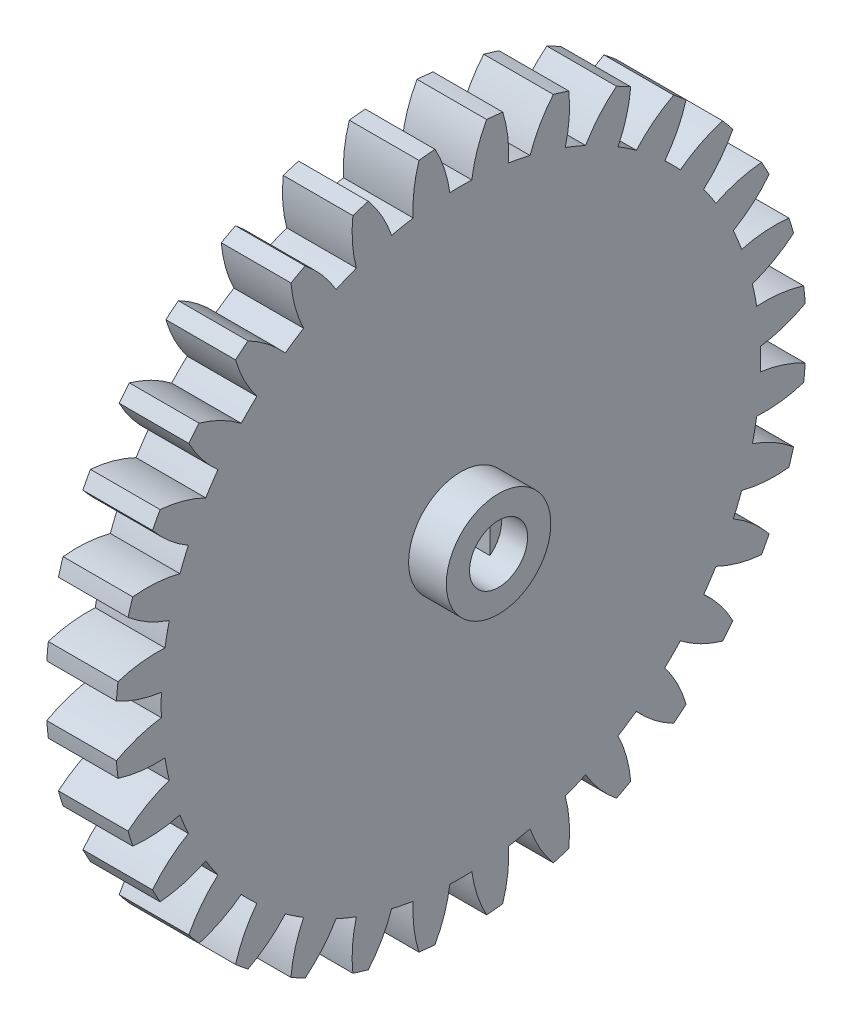
SolidWorks part; units mm, degrees
ref_plane "Plane1" through (0, 0, 0) normal (0, 0, 1) x (1, 0, 0)
ref_plane "Plane2" through (0, 0, 0) normal (0, 1, 0) x (1, 0, 0)
ref_plane "Plane3" through (0, 0, 0) normal (1, 0, 0) x (0, 0, -1)
sketch "HoldingSke" plane through (0, 0, 0) normal (0, 1, 0) x (1, 0, 0)
  line L0 (0, 0) -> (0.4846, -0.3028)
  line L1 (-15, 0) -> (100, 0) construction
  line L2 (0, 0) -> (-2.1039, 2.3779)
  line L3 (0, 0) -> (-11.863, 4.5341)
  line L4 (0, 0) -> (7.3237, 4.5764)
  line L5 (0, 0) -> (-46.8476, -17.4728)
  line L6 (0, 0) -> (-4.9738, -3.3558)
  line L7 (-2.1039, 2.3779) -> (8.6586, 51.2059)
  line L8 (-76.2, 54.61) -> (-76.1, 54.61)
  line L9 (-67.7845, 28.3722) -> (-49.3413, 33.142)
  line L10 (-76.2, 71.12) -> (104.1128, 71.12)
  line L11 (0, 0) -> (-6, 0)
  line L12 (-76.2, 101.6) -> (-76.147, 101.6)
  line L13 (24.9733, 27.94) -> (52.9518, 28.4284)
  line L14 (24.9733, 27.94) -> (24.9743, 27.94)
  line L15 (24.9733, 27.94) -> (100.4006, 29.5858)
  line L16 (-63.627, -1.75) -> (-12.827, -1.75)
  circle A0 centre (0, 0) radius 0.4
  circle A1 centre (0, 0) radius 25.8115
  circle A2 centre (0, 0) radius 37.5
  circle A3 centre (0, 0) radius 0.4
  dimension "MHD" = 51.623
  dimension "Hub_dia" = 75
  dimension "Bore" = 0.8
  dimension "MBD" = 0.8
  dimension "Num_teeth" = 32
  dimension "Pitch" = 0.5714
  dimension "Overall_len" = 50
  dimension "Show_teeth" = 32
  dimension "Thickness" = 6
  dimension "OAL" = 50.0001
  dimension "T_dim" = 0.1
  dimension "Ap" = 14.5
  dimension "H" = 19.05
  dimension "Pitch_radius" = 180.3128
  dimension "Width" = 6
  dimension "Backlash" = 0.053
  dimension "Addendum_fac" = 1
  dimension "Dedendum_fac" = 1.25
  dimension "Clearance_fac" = 0.25
  dimension "Dedendum_add" = 0.001
  dimension "Module" = 1.75
sketch "BasProSke" plane through (0, 0, 0) normal (0, 1, 0) x (1, 0, 0)
  line L0 (-10, 0) -> (60, 0) construction
  line L1 (0, 0) -> (0, 29.75)
  line L2 (0, 0) -> (6, 0)
  line L3 (6, 0) -> (6, 29.75)
  line L4 (6, 29.75) -> (0, 29.75)
  dimension "Thickness" = 6
  dimension "Diameter" = 59.5
revolve "Base-Revolve" add sketch "BasProSke" angle 360 about L0
sketch "TooCutSke" plane through (0, 0, 0) normal (1, 0, 0) x (0, 0, -1)
  line L1 (0, 0) -> (0, 107) construction
  line L2 (0, 0) -> (-1.4666, 27.9616) construction
  line L3 (0, 0) -> (-5.4832, 55.672) construction
  line L4 (-1.4666, 27.9616) -> (-2.7416, 27.836) construction
  arc A0 (0.9481, 25.7941) -> (-0.9481, 25.7941) centre (0, 0) ccw
  arc A1 (2.2372, 29.6912) -> (-2.2372, 29.6912) centre (0, 0) ccw
  circle A2 centre (0, 0) radius 28 construction
  circle A3 centre (0, 0) radius 27.1081 construction
  arc A4 (-0.9481, 25.7941) -> (-2.2372, 29.6912) centre (-12.0459, 24.2847) ccw
  arc A5 (2.2372, 29.6912) -> (0.9481, 25.7941) centre (12.0459, 24.2847) ccw
  dimension "Root_dia" = 51.623
  dimension "Overcut_dia" = 59.5508
  dimension "Pitch_dia" = 56
  dimension "Base_dia" = 54.2163
  dimension "Flank_rad" = 11.2
  dimension "Half_ang" = 5.625
  dimension "Half_CT" = 1.2811
extrude "ToothCut" cut sketch "TooCutSke" along normal through all
fillet "Breaks" [suppressed] radius 0.035
fillet "RootFillets" [suppressed] radius 0.4385
pattern_circular "TeethCuts" count 32 every 11.25 about axis through (-10, 0, 0) along (1, 0, 0) of "ToothCut", "RootFillets", "Breaks"
sketch "HubNeaOneSke" plane through (0, 0, 0) normal (-1, 0, 0) x (0, 0, 1)
  circle A0 centre (0, 0) radius 25.8115
  dimension "Diameter" = 51.623
extrude "HubNearOne" [suppressed] add sketch "HubNeaOneSke" along normal blind 44.0001
sketch "HubNeaBotSke" plane through (0, 0, 0) normal (-1, 0, 0) x (0, 0, 1)
  circle A0 centre (0, 0) radius 25.8115
  dimension "Diameter" = 51.623
extrude "HubNearBoth" [suppressed] add sketch "HubNeaBotSke" along normal blind 22
ref_plane "FarPln" through (6, 0, 0) normal (1, 0, 0) x (0, 0, -1)
sketch "HubFarSke" plane through (6, 0, 0) normal (1, 0, 0) x (0, 0, -1)
  circle A0 centre (0, 0) radius 25.8115
  dimension "Diameter" = 51.623
extrude "HubFar" [suppressed] add sketch "HubFarSke" along normal blind 22
sketch "BorSke" plane through (0, 0, 0) normal (1, 0, 0) x (0, 0, -1)
  circle A0 centre (0, 0) radius 0.4
  dimension "Diameter" = 0.8
extrude "Bore" cut sketch "BorSke" along normal mid plane 100.0001
sketch "KeySke" plane through (0, 0, 0) normal (1, 0, 0) x (0, 0, -1)
  line L0 (-0.05, 0) -> (-0.05, 0.5)
  line L1 (-0.05, 0.5) -> (0.05, 0.5)
  line L2 (0.05, 0.5) -> (0.05, 0)
  line L3 (0, 0) -> (0, 34) construction
  line L4 (-0.05, 0) -> (0.05, 0)
  dimension "Offset" = 0.5
  dimension "Width" = 0.1
extrude "Keyway" [suppressed] cut sketch "KeySke" along normal mid plane 100.0001
pattern_circular "Keyway2" [suppressed] count 2 every 90 about axis through (-10, 0, 0) along (1, 0, 0)
sketch "Sketch2" plane through (6, 0, 0) normal (1, 0, 0) x (0, 0, -1)
  circle A0 centre (0, 0) radius 4.5
  dimension "D1" = 9
extrude "Boss-Extrude1" add sketch "Sketch2" along normal blind 3.25
sketch "Sketch3" plane through (9.25, 0, 0) normal (1, 0, 0) x (0, 0, -1)
  circle A0 centre (0, 0) radius 2.5
extrude "Cut-Extrude1" cut sketch "Sketch3" against normal blind 2.25
sketch "Sketch5" plane through (7, 0, 0) normal (1, 0, 0) x (0, 0, -1)
  line L0 (-1.4999, 2.0001) -> (-1.5001, -1.9999)
  line L1 (1.5001, 1.9999) -> (1.4999, -2.0001)
  circle A0 centre (0, 0) radius 2.5
  circle M3 centre (0, 0) radius 2.5
  dimension "D1" = 5
  dimension "D2" = 3
extrude "Cut-Extrude3" cut sketch "Sketch5" against normal blind 6 contours L1 L0 M3
equation "' \"Module@HoldingSke\" = 6.35"
equation "' \"Num_teeth@HoldingSke\" = 12"
equation "' \"Ap@HoldingSke\" =  20"
equation "' \"Ap@HoldingSke\" = 20"
equation "' \"Width@HoldingSke\" = 0.5 * 25.4"
equation "' \"Hub_dia@HoldingSke\"= 1 * 25.4"
equation "' \"Hub_dia@HoldingSke\" = 1 * 25.4"
equation "' \"Overall_len@HoldingSke\" = 1.0 * 25.4"
equation "' \"Bore@HoldingSke\" = 0.75 * 25.4"
equation "' \"T_dim@HoldingSke\" = 0.1 * 25.4"
equation "' \"Width@KeySke\" = 0.25 * 25.4"
equation "' \"Show_teeth@HoldingSke\" = 13"
equation "' \"Backlash@HoldingSke\" = 0.009 * 25.4"
equation "' \"Addendum_fac@HoldingSke\" = 1.0"
equation "' \"Dedendum_fac@HoldingSke\" = 1.25"
equation "' \"Dedendum_add@HoldingSke\" = 0.00005 * 25.4"
equation "' \"Clearance_fac@HoldingSke\" = 0.25"
equation "\"Pitch@HoldingSke\" = 1 / \"Module@HoldingSke\""
equation "\"Overcut_dia@TooCutSke\" = (\"Num_teeth@HoldingSke\" + 2 * \"Addendum_fac@HoldingSke\") / \"Pitch@HoldingSke\" + 0.002 * 25.4"
equation "\"Pitch_dia@TooCutSke\" = \"Num_teeth@HoldingSke\" / \"Pitch@HoldingSke\""
equation "\"Base_dia@TooCutSke\" = \"Num_teeth@HoldingSke\" / \"Pitch@HoldingSke\" * cos((\"Ap@HoldingSke\"  * 3.14159265 / 180))"
equation "\"Root_dia@TooCutSke\" = (\"Num_teeth@HoldingSke\" + 2) / \"Pitch@HoldingSke\" - 2 * (\"Addendum_fac@HoldingSke\" + \"Dedendum_fac@HoldingSke\") / \"Pitch@HoldingSke\" - \"Dedendum_add@HoldingSke\" * 2"
equation "\"Half_ang@TooCutSke\" = 180 / \"Num_teeth@HoldingSke\""
equation "\"Half_CT@TooCutSke\" = \"Num_teeth@HoldingSke\" / \"Pitch@HoldingSke\" * sin((3.14159265 / 2 / \"Num_teeth@HoldingSke\")) / 2 - 7 * \"Backlash@HoldingSke\" / 4"
equation "\"Flank_rad@TooCutSke\" = \"Num_teeth@HoldingSke\" / \"Pitch@HoldingSke\" / 5"
equation "\"Radius@RootFillets\" = \"Clearance_fac@HoldingSke\" / \"Pitch@HoldingSke\" + \"Dedendum_add@HoldingSke\""
equation "\"Break_rad@Breaks\" = 0.02 / \"Pitch@HoldingSke\""
equation "\"Thickness@HoldingSke\" = \"Width@HoldingSke\""
equation "\"OAL@HoldingSke\" = \"Thickness@HoldingSke\""
equation "\"MHD@HoldingSke\" = (\"Num_teeth@HoldingSke\" + 2) / \"Pitch@HoldingSke\" - 2 * (\"Addendum_fac@HoldingSke\" + \"Dedendum_fac@HoldingSke\")  / \"Pitch@HoldingSke\" - \"Dedendum_add@HoldingSke\" * 2"
equation "\"MBD@HoldingSke\" = (\"Num_teeth@HoldingSke\" + 2) / \"Pitch@HoldingSke\" - 2 * (\"Addendum_fac@HoldingSke\" + \"Dedendum_fac@HoldingSke\")  / \"Pitch@HoldingSke\" - \"Dedendum_add@HoldingSke\" * 2 - 0.002 * 25.4"
equation "\"MHD@HoldingSke\" = ((sgn( \"MHD@HoldingSke\" - \"Hub_dia@HoldingSke\" )-1)*( \"MHD@HoldingSke\" - \"Hub_dia@HoldingSke\" ))/-2+ \"Hub_dia@HoldingSke\""
equation "\"MBD@HoldingSke\" = ((sgn( \"MBD@HoldingSke\" - \"Bore@HoldingSke\" )-1)*( \"MBD@HoldingSke\" - \"Bore@HoldingSke\" ))/-2+ \"Bore@HoldingSke\""
equation "\"OAL@HoldingSke\" = ((sgn( \"OAL@HoldingSke\" - \"Overall_len@HoldingSke\" )+1)*( \"OAL@HoldingSke\" - \"Overall_len@HoldingSke\" ))/2 + \"Overall_len@HoldingSke\" + 0.000002 * 25.4"
equation "\"Num_teeth@TeethCuts\" = int( \"Show_teeth@HoldingSke\" ) + 1"
equation "\"Num_teeth@TeethCuts\" = ((sgn( \"Num_teeth@TeethCuts\" - \"Num_teeth@HoldingSke\" )-1)*( \"Num_teeth@TeethCuts\" - \"Num_teeth@HoldingSke\" ))/-2+ \"Num_teeth@HoldingSke\""
equation "\"Num_teeth@TeethCuts\" = ((sgn( \"Num_teeth@TeethCuts\" - 2.0)+1)*( \"Num_teeth@TeethCuts\" - 2.0))/2 +2.0"
equation "\"Angle@TeethCuts\" = 360.0 / \"Num_teeth@HoldingSke\""
equation "\"Diameter@BasProSke\" = (\"Num_teeth@HoldingSke\" + 2 * \"Addendum_fac@HoldingSke\") / \"Pitch@HoldingSke\""
equation "\"Thickness@BasProSke\"  = \"Thickness@HoldingSke\""
equation "' \"Fillet_rad@BasProSke\" =  \"Thickness@HoldingSke\" * 0.05"
equation "' \"Fillet_rad@BasProSke\" = \"Thickness@HoldingSke\" * 0.05"
equation "\"MHD@HoldingSke\" = ((sgn( \"MHD@HoldingSke\" - \"Root_dia@TooCutSke\" )-1)*( \"MHD@HoldingSke\" - \"Root_dia@TooCutSke\" ))/-2+ \"Root_dia@TooCutSke\""
equation "\"Diameter@HubNeaOneSke\" = \"MHD@HoldingSke\""
equation "\"Length@HubNearOne\" = \"OAL@HoldingSke\" - \"Thickness@BasProSke\""
equation "\"Diameter@HubNeaBotSke\" = \"MHD@HoldingSke\""
equation "\"Length@HubNearBoth\" = ( \"OAL@HoldingSke\" - \"Thickness@BasProSke\" ) / 2.0"
equation "\"Thickness@FarPln\" = \"Thickness@BasProSke\""
equation "\"Diameter@HubFarSke\" = \"MHD@HoldingSke\""
equation "\"Length@HubFar\" = ( \"OAL@HoldingSke\" - \"Thickness@BasProSke\" ) / 2.0"
equation "\"Diameter@BorSke\" = \"MBD@HoldingSke\""
equation "\"D1@Bore\" = \"OAL@HoldingSke\" * 2.0"
equation "\"D1@Keyway\" = \"OAL@HoldingSke\" * 2.0"
equation "\"Offset@KeySke\" = \"T_dim@HoldingSke\" + \"MBD@HoldingSke\" / 2.0"
